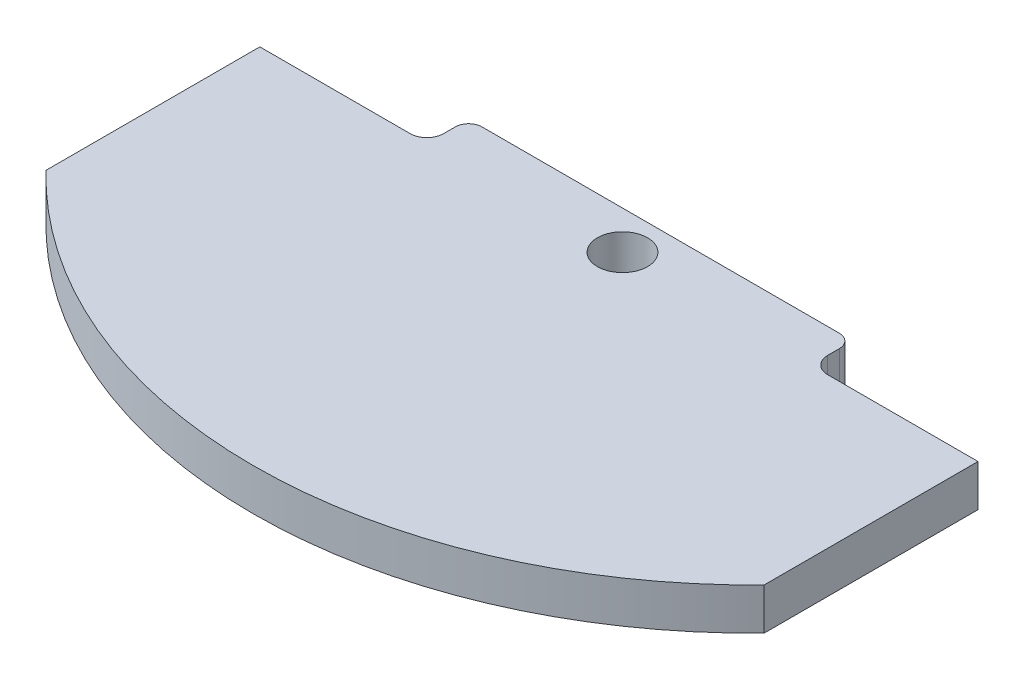
SolidWorks part; units mm, degrees
ref_plane "Front Plane" through (0, 0, 0) normal (0, 0, 1) x (1, 0, 0)
ref_plane "Top Plane" through (0, 0, 0) normal (0, 1, 0) x (1, 0, 0)
ref_plane "Right Plane" through (0, 0, 0) normal (1, 0, 0) x (0, 0, -1)
sketch "Sketch6" plane through (0, 0, 0) normal (0, 1, 0) x (1, 0, 0)
  line L1 (0, 0) -> (109.1946, 0)
  line L2 (0, 0) -> (0, -38.862)
  line L4 (109.1946, 0) -> (109.1946, -38.862)
  arc A0 (109.1946, -38.862) -> (0, -38.862) centre (54.5973, 14.007) cw
  dimension "D2" = 38.862
  dimension "D1" = 109.1946
extrude "Boss-Extrude2" add sketch "Sketch6" along normal blind 6.35
sketch "Sketch10" plane through (0, 6.35, 0) normal (0, 1, 0) x (1, 0, 0)
  line L0 (54.5973, 0) -> (54.5973, -61.993) construction
  line L1 (109.1946, 0) -> (0, 0) construction
  line L2 (109.1946, -6.35) -> (83.7946, -6.35)
  line L3 (0, 0) -> (25.4, 0)
  line L4 (0, 0) -> (0, -6.35)
  line L5 (0, -6.35) -> (25.4, -6.35)
  line L6 (25.4, 0) -> (25.4, -6.35)
  line L7 (83.7946, 0) -> (83.7946, -6.35)
  line L8 (109.1946, 0) -> (83.7946, 0)
  line L9 (109.1946, 0) -> (109.1946, -6.35)
  arc A0 (0, -38.862) -> (109.1946, -38.862) centre (54.5973, 14.007) ccw construction
  dimension "D1" = 25.4
  dimension "D2" = 6.35
extrude "Cut-Extrude1" cut sketch "Sketch10" against normal through all
fillet "Fillet1" radius 2.54 2 edges at (83.7946, 3.175, 6.35) (25.4, 3.175, 6.35)
fillet "Fillet2" radius 2.032 2 edges at (83.7946, 3.175, 0) (25.4, 3.175, 0)
sketch "Sketch11" plane through (0, 0, 0) normal (0, -1, 0) x (1, 0, 0)
  line L0 (25.4, 3.81) -> (25.4, 2.032) construction
  circle A3 centre (54.61, 5.8194) radius 3.81
  dimension "D1" = 29.21
extrude "Cut-Extrude2" cut sketch "Sketch11" against normal through all
